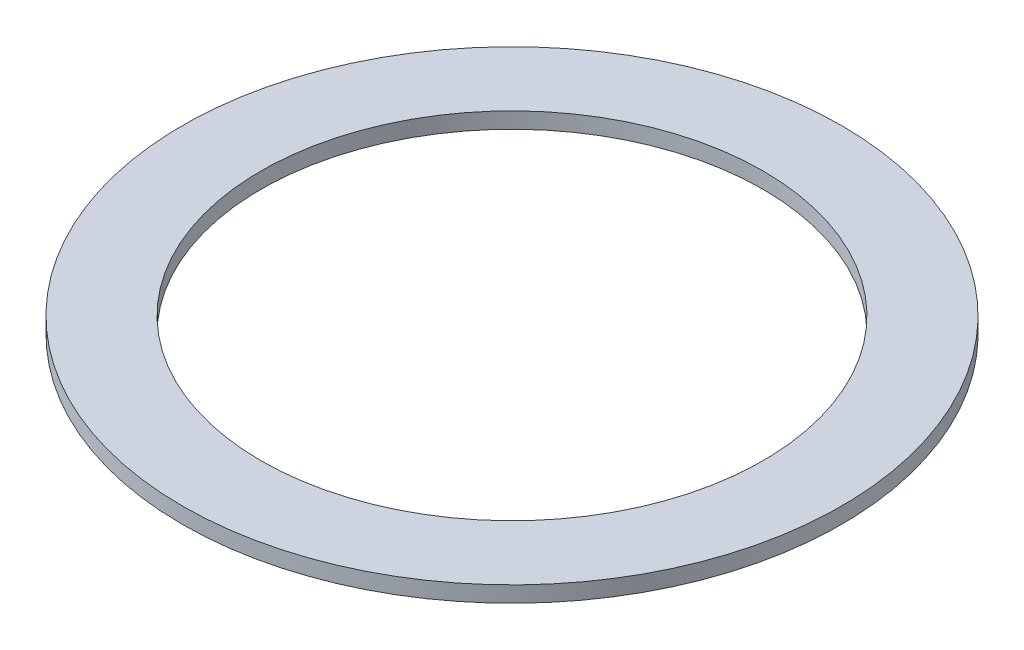
SolidWorks part; units mm, degrees
material "Plain Carbon Steel"
ref_plane "Front Plane" through (0, 0, 0) normal (0, 0, 1) x (1, 0, 0)
ref_plane "Top Plane" through (0, 0, 0) normal (0, 1, 0) x (1, 0, 0)
ref_plane "Right Plane" through (0, 0, 0) normal (1, 0, 0) x (0, 0, -1)
sketch "Sketch1" plane through (0, 0, 0) normal (0, 1, 0) x (1, 0, 0)
  circle A0 centre (0, 0) radius 6.0071
  circle A1 centre (0, 0) radius 7.8867
  dimension "D1" = 12.0142
  dimension "D2" = 15.7734
extrude "Boss-Extrude1" add sketch "Sketch1" along normal blind 0.381
